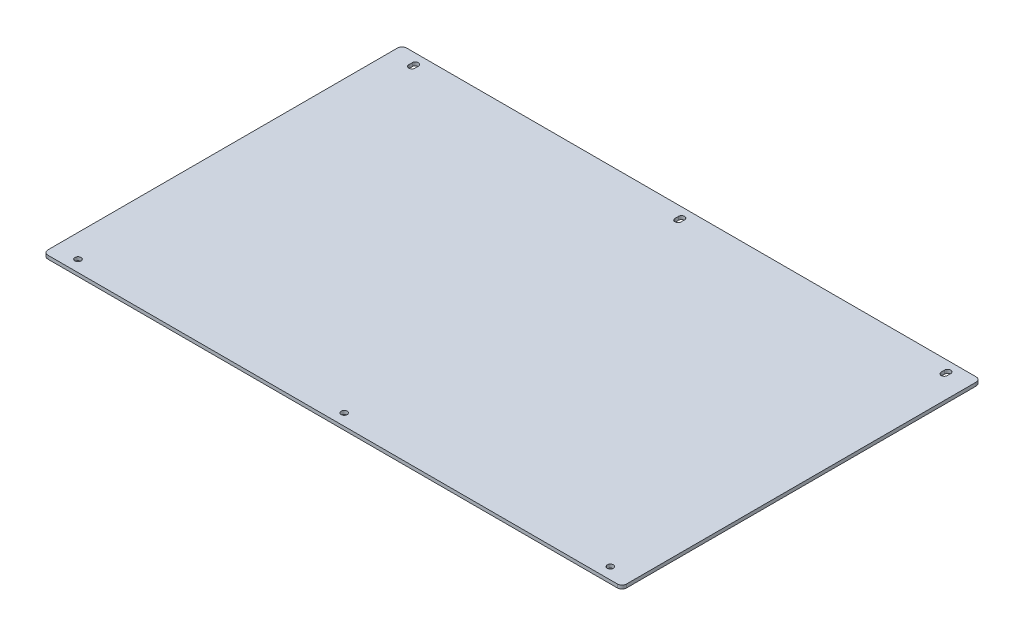
SolidWorks part; units mm, degrees
ref_plane "Front Plane" through (0, 0, 0) normal (0, 0, 1) x (1, 0, 0)
ref_plane "Top Plane" through (0, 0, 0) normal (0, 1, 0) x (1, 0, 0)
ref_plane "Right Plane" through (0, 0, 0) normal (1, 0, 0) x (0, 0, -1)
sketch "Sketch1" plane through (0, 0, 0) normal (0, 1, 0) x (1, 0, 0)
  line L1 (-250, -155) -> (250, -155)
  line L2 (-250, -155) -> (-250, 155)
  line L3 (-250, 155) -> (250, 155)
  line L4 (250, -155) -> (250, 155)
  line L5 (-250, -155) -> (250, 155) construction
  line L6 (-250, 155) -> (250, -155) construction
  point P0 (0, 0)
  dimension "D1" = 500
  dimension "D2" = 310
extrude "Boss-Extrude1" add sketch "Sketch1" along normal blind 3
fillet "Fillet1" radius 4 4 edges at (-250, 1.5, 155) (-250, 1.5, -155) (250, 1.5, -155) (250, 1.5, 155)
hole_wizard "Ø5.3 (5.3) Diameter Hole1" positions "Sketch4" profile "Sketch5" hole size "Ø5.3" standard "ANSI Metric" end condition through all
sketch "Sketch4" plane through (0, 3, 0) normal (0, 1, 0) x (1, 0, 0)
  line L1 (-230, -145) -> (230, -145)
  line L2 (-230, -145) -> (-230, 145)
  line L3 (-230, 145) -> (230, 145)
  line L4 (230, -145) -> (230, 145)
  line L5 (-230, -145) -> (230, 145) construction
  line L6 (-230, 145) -> (230, -145) construction
  line L7 (246, 155) -> (-246, 155) construction
  line L8 (250, -151) -> (250, 151) construction
  point P2 (230, 145)
  point P59 (-230, -145)
  point P60 (-230, 145)
  point P61 (230, -145)
  point P68 (0, 145)
  point P70 (0, -145)
  dimension "D1" = 10
  dimension "D2" = 20
sketch "Sketch5" plane through (230, 3, -145) normal (1, 0, 0) x (0, 0, 1)
  line L0 (0, 0) -> (0, 3)
  line L1 (0, 3) -> (2.65, 3)
  line L2 (2.65, 3) -> (2.65, 0)
  line L5 (2.65, 0) -> (0, 0)
  line L11 (0, -6.35) -> (0, 107.95) construction
  dimension "Thru Hole Dia." = 5.3
  dimension "Thru Hole Depth" = 3
sketch "Sketch6" plane through (0, 3, 0) normal (0, 1, 0) x (1, 0, 0)
  line L1 (-200, -145) -> (200, -145) construction
  line L2 (-200, -145) -> (-200, 145) construction
  line L3 (-200, 145) -> (200, 145) construction
  line L4 (200, -145) -> (200, 145) construction
  line L5 (-200, -145) -> (200, 145) construction
  line L6 (-200, 145) -> (200, -145) construction
  circle A0 centre (-200, 145) radius 2.6
  circle A1 centre (200, 145) radius 2.6
  circle A2 centre (200, -145) radius 2.6
  circle A3 centre (-200, -145) radius 2.6
  point P0 (0, 0)
  dimension "D3" = 5.2
  dimension "D1" = 290
  dimension "D2" = 400
extrude "Cut-Extrude1" [suppressed] cut sketch "Sketch6" against normal through all
sketch "Sketch7" plane through (0, 3, 0) normal (0, 1, 0) x (1, 0, 0)
  line L0 (-230, 143.5) -> (-230, 146.5) construction
  line L1 (-232.65, 143.5) -> (-232.65, 146.5)
  line L2 (-227.35, 143.5) -> (-227.35, 146.5)
  line L3 (0, 143.5) -> (0, 146.5) construction
  line L4 (-2.65, 143.5) -> (-2.65, 146.5)
  line L5 (2.65, 143.5) -> (2.65, 146.5)
  line L6 (230, 143.5) -> (230, 146.5) construction
  line L7 (227.35, 143.5) -> (227.35, 146.5)
  line L8 (232.65, 143.5) -> (232.65, 146.5)
  arc A0 (-232.65, 143.5) -> (-227.35, 143.5) centre (-230, 143.5) ccw
  arc A1 (-227.35, 146.5) -> (-232.65, 146.5) centre (-230, 146.5) ccw
  circle A2 centre (-230, 145) radius 2.65 construction
  arc A3 (-2.65, 143.5) -> (2.65, 143.5) centre (0, 143.5) ccw
  arc A4 (2.65, 146.5) -> (-2.65, 146.5) centre (0, 146.5) ccw
  arc A5 (227.35, 143.5) -> (232.65, 143.5) centre (230, 143.5) ccw
  arc A6 (232.65, 146.5) -> (227.35, 146.5) centre (230, 146.5) ccw
  point P2 (-230, 145)
  point P10 (0, 145)
  point P14 (0, 145)
  point P21 (230, 145)
  dimension "D1" = 3
  dimension "D2" = 3
extrude "Cut-Extrude2" cut sketch "Sketch7" against normal through all
